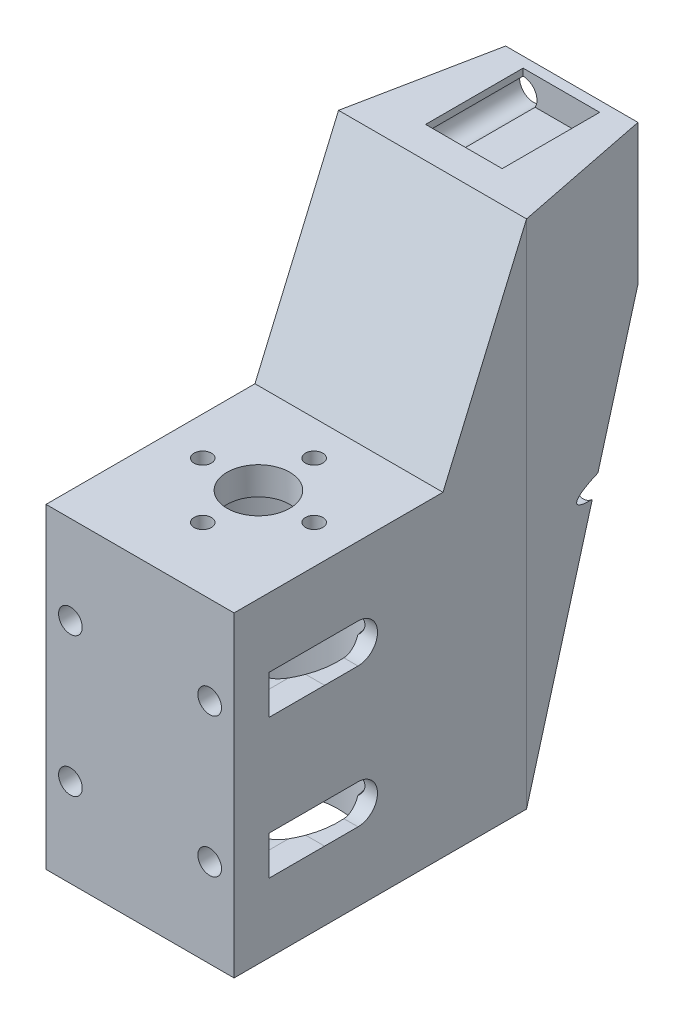
SolidWorks part; units mm, degrees
ref_plane "Front Plane" through (0, 0, 0) normal (0, 0, 1) x (1, 0, 0)
ref_plane "Top Plane" through (0, 0, 0) normal (0, 1, 0) x (1, 0, 0)
ref_plane "Right Plane" through (0, 0, 0) normal (1, 0, 0) x (0, 0, -1)
sketch "Sketch1" plane through (0, 0, 0) normal (0, 1, 0) x (1, 0, 0)
  line L0 (0, -1000) -> (0, 49000) construction
  line L2 (-13.5, -17) -> (13.5, -17)
  line L3 (-13.5, -17) -> (-13.5, 45)
  line L4 (-13.5, 45) -> (13.5, 45)
  line L5 (13.5, -17) -> (13.5, 45)
  line L6 (-5.5, 43.5) -> (5.5, 43.5) construction
  line L7 (-5.5, 43.5) -> (-5.5, 29.5) construction
  line L8 (-5.5, 29.5) -> (5.5, 29.5) construction
  line L9 (5.5, 43.5) -> (5.5, 29.5) construction
  circle A0 centre (0, 0) radius 11 construction
  circle A1 centre (0, 37) radius 5 construction
  point P9 (0, -17)
  dimension "D1" = 22
  dimension "D4" = 37
  dimension "D2" = 17
  dimension "D3" = 27
  dimension "D5" = 8
  dimension "D6" = 11
  dimension "D7" = 14
  dimension "D8" = 1.5
  dimension "D9" = 5.5
extrude "Boss-Extrude1" add sketch "Sketch1" against normal blind 73.4 contours L2 L5 L4 L3
sketch "Sketch2" plane through (0, 0, -45) normal (0, 0, -1) x (-1, 0, 0)
  line L0 (0, -1000) -> (0, 49000) construction
  line L1 (-24.4686, -3) -> (24.4686, -3) construction
  line L2 (5.5, 0) -> (-5.5, 0) construction
  circle A0 centre (-5.5, -3) radius 2
  circle A1 centre (5.5, -3) radius 2
  point P6 (0, -3)
  dimension "D1" = 3
  dimension "D2" = 4
  dimension "D3" = 5.5
extrude "Cut-Extrude1" cut sketch "Sketch2" against normal blind 20
sketch "Sketch4" plane through (0, 0, 0) normal (0, 1, 0) x (1, 0, 0)
  line L1 (5.5, 43.5) -> (-5.5, 43.5)
  line L2 (5.5, 43.5) -> (5.5, 29.5)
  line L3 (5.5, 29.5) -> (-5.5, 29.5)
  line L4 (-5.5, 43.5) -> (-5.5, 29.5)
extrude "Cut-Extrude2" cut sketch "Sketch4" against normal blind 4
sketch "Sketch5" plane through (0, 0, 0) normal (0, 1, 0) x (1, 0, 0)
  circle A0 centre (0, 0) radius 4.5
extrude "Cut-Extrude3" cut sketch "Sketch5" against normal through all
sketch "Sketch6" plane through (0, 0, 0) normal (0, 1, 0) x (1, 0, 0)
  circle A0 centre (0, 0) radius 11.5
extrude "Cut-Extrude4" cut sketch "Sketch6" against normal through all from offset 32 offset against normal yes
sketch "Sketch7" plane through (13.5, 0, 0) normal (1, 0, 0) x (0, 0, -1)
  line L0 (-17, -28) -> (13, -28)
  line L1 (-17, -73.4) -> (-17, 0) construction
  line L2 (13, -28) -> (25, 0)
  line L3 (-17, 0) -> (45, 0) construction
  line L4 (25, 0) -> (-17, 0)
  line L5 (-17, 0) -> (-17, -28)
  line L6 (-17, -73.4) -> (45, -73.4) construction
  dimension "D1" = 20
  dimension "D2" = 30
  dimension "D3" = 45.4
extrude "Cut-Extrude5" cut sketch "Sketch7" against normal through all
hole_wizard "M3 Clearance Hole1" positions "Sketch10" profile "Sketch11" hole size "M3" standard "ANSI Metric" end condition through all
sketch "Sketch10" plane through (0, 0, 17) normal (0, 0, 1) x (1, 0, 0)
  line L0 (-13.5, -73.4) -> (-13.5, -28) construction
  line L1 (-13.5, -73.4) -> (13.5, -73.4) construction
  point P0 (-10, -60.7)
  point P8 (10, -60.7)
  point P9 (10, -40.7)
  point P10 (-10, -40.7)
  dimension "D3" = 3.5
  dimension "D4" = 12.7
  dimension "D1" = 2
  dimension "D2" = 2
sketch "Sketch11" plane through (-10, -60.7, 17) normal (1, 0, 0) x (0, -1, 0)
  line L0 (0, 0) -> (0, 62)
  line L1 (0, 62) -> (1.7, 62)
  line L2 (1.7, 62) -> (1.7, 0)
  line L5 (1.7, 0) -> (0, 0)
  line L11 (0, -6.35) -> (0, 107.95) construction
  dimension "Thru Hole Dia." = 3.4
  dimension "Thru Hole Depth" = 62
sketch "Sketch12" plane through (0, 0, 17) normal (0, 0, 1) x (1, 0, 0)
  line L0 (-10, -63.5) -> (-13.68, -63.5)
  line L1 (-13.68, -63.5) -> (-13.68, -57.9)
  line L2 (-13.68, -57.9) -> (-10, -57.9)
  line L3 (-13.68, -43.5) -> (-13.68, -37.9)
  line L4 (-13.68, -37.9) -> (-10, -37.9)
  line L5 (-10, -43.5) -> (-13.68, -43.5)
  line L6 (0, -1028) -> (0, 48972) construction
  line L7 (-13.5, -28) -> (13.5, -28) construction
  line L8 (10, -43.5) -> (13.68, -43.5)
  line L9 (13.68, -37.9) -> (10, -37.9)
  line L10 (13.68, -43.5) -> (13.68, -37.9)
  line L11 (13.68, -57.9) -> (10, -57.9)
  line L12 (13.68, -63.5) -> (13.68, -57.9)
  line L13 (10, -63.5) -> (13.68, -63.5)
  arc A0 (-10, -63.5) -> (-10, -57.9) centre (-10, -60.7) ccw
  arc A1 (-10, -43.5) -> (-10, -37.9) centre (-10, -40.7) ccw
  arc A2 (10, -43.5) -> (10, -37.9) centre (10, -40.7) cw
  arc A3 (10, -63.5) -> (10, -57.9) centre (10, -60.7) cw
  point P16 (0, -28)
  dimension "D1" = 2
extrude "Cut-Extrude6" cut sketch "Sketch12" against normal blind 8 from offset 5 offset against normal yes
sketch "Sketch13" plane through (0, 0, 0) normal (0, 1, 0) x (1, 0, 0)
  line L0 (-13.5, 25) -> (-9.5, 45)
  line L1 (-9.5, 45) -> (-13.5, 45)
  line L2 (-13.5, 45) -> (-13.5, 25)
  line L3 (-13.5, 45) -> (13.5, 45) construction
  line L4 (0, -955) -> (0, 49045) construction
  line L6 (13.5, 45) -> (13.5, 25)
  line L7 (9.5, 45) -> (13.5, 45)
  line L8 (13.5, 25) -> (9.5, 45)
  point P12 (0, 45)
  dimension "D1" = 4
extrude "Cut-Extrude7" cut sketch "Sketch13" against normal through all
hole_wizard "Tap Drill for M3x0.5 Tap1" positions "Sketch14" profile "Sketch15" hole size "M3x0.5" standard "ANSI Metric"
sketch "Sketch14" plane through (0, -28, 0) normal (0, 1, 0) x (1, 0, 0)
  point P0 (0, -8)
  point P10 (-8, 0)
  point P11 (0, 8)
  point P12 (8, 0)
  point P13 (0, 0)
  dimension "D1" = 8
  dimension "D2" = 4
sketch "Sketch15" plane through (0, -28, 8) normal (1, 0, 0) x (0, 0, 1)
  line L0 (0, 0) -> (0, 45.4)
  line L1 (0, 45.4) -> (1.25, 45.4)
  line L2 (1.25, 45.4) -> (1.25, 0)
  line L5 (1.25, 0) -> (0, 0)
  line L11 (0, -6.35) -> (0, 107.95) construction
  dimension "Thru Hole Dia." = 2.5
  dimension "Thru Hole Depth" = 45.4
sketch "Sketch16" plane through (13.5, 0, 0) normal (1, 0, 0) x (0, 0, -1)
  line L0 (-4, -40.7) -> (0.7984, -40.7) construction
  line L1 (-4, -43.5) -> (-4, -37.9) construction
  line L2 (-4, -37.9001) -> (0.7984, -37.9001)
  line L3 (-4, -43.4999) -> (0.7984, -43.4999)
  line L4 (-4, -60.7) -> (0.7984, -60.7) construction
  line L5 (-4, -57.9001) -> (0.7984, -57.9001)
  line L6 (-4, -63.4999) -> (0.7984, -63.4999)
  arc A0 (-4, -37.9001) -> (-4, -43.4999) centre (-4, -40.7) ccw
  arc A1 (0.7984, -43.4999) -> (0.7984, -37.9001) centre (0.7984, -40.7) ccw
  arc A2 (-4, -57.9001) -> (-4, -63.4999) centre (-4, -60.7) ccw
  arc A3 (0.7984, -63.4999) -> (0.7984, -57.9001) centre (0.7984, -60.7) ccw
  point P4 (-1.6008, -40.7)
  point P12 (-1.6008, -60.7)
  dimension "D1" = 2
extrude "Cut-Extrude8" cut sketch "Sketch16" against normal through all
hole_wizard "CSK for M2 Flat Head Machine Screw1" positions "Sketch17" profile "Sketch19" countersink size "M2" standard "ANSI Metric"
sketch "Sketch17" plane through (0, 0, -45) normal (0, 0, -1) x (-1, 0, 0)
  line L0 (9.5, 0) -> (-9.5, 0) construction
  point P0 (0, -11)
  dimension "D1" = 11
sketch "Sketch19" plane through (0, -11, -45) normal (1, 0, 0) x (0, 1, 0)
  line L0 (0, 0) -> (0, 7.6223)
  line L1 (0, 7.6223) -> (2.7, 6)
  line L2 (2.7, 6) -> (2.7, 0.1428)
  line L3 (2.7, 0.1428) -> (2.8, 0)
  line L5 (2.8, 0) -> (0, 0)
  line L6 (-2.7, 0.1428) -> (-2.8, 0) construction
  line L10 (0, 7.6223) -> (-2.7, 6) construction
  line L11 (0, -6.35) -> (0, 107.95) construction
  dimension "Hole Dia." = 5.4
  dimension "Hole Depth" = 6
  dimension "Near C'Sink Dia." = 5.6
  dimension "Near C'Sink Angle" = 70
  dimension "Drill Angle" = 118
sketch "Sketch20" plane through (13.5, 0, 0) normal (1, 0, 0) x (0, 0, -1)
  line L0 (25, -73.4) -> (47.1285, -73.4)
  line L1 (47.1285, -73.4) -> (47.1285, -14.4528)
  line L2 (47.1285, -14.4528) -> (25, -73.4)
extrude "Cut-Extrude9" cut sketch "Sketch20" against normal through all
